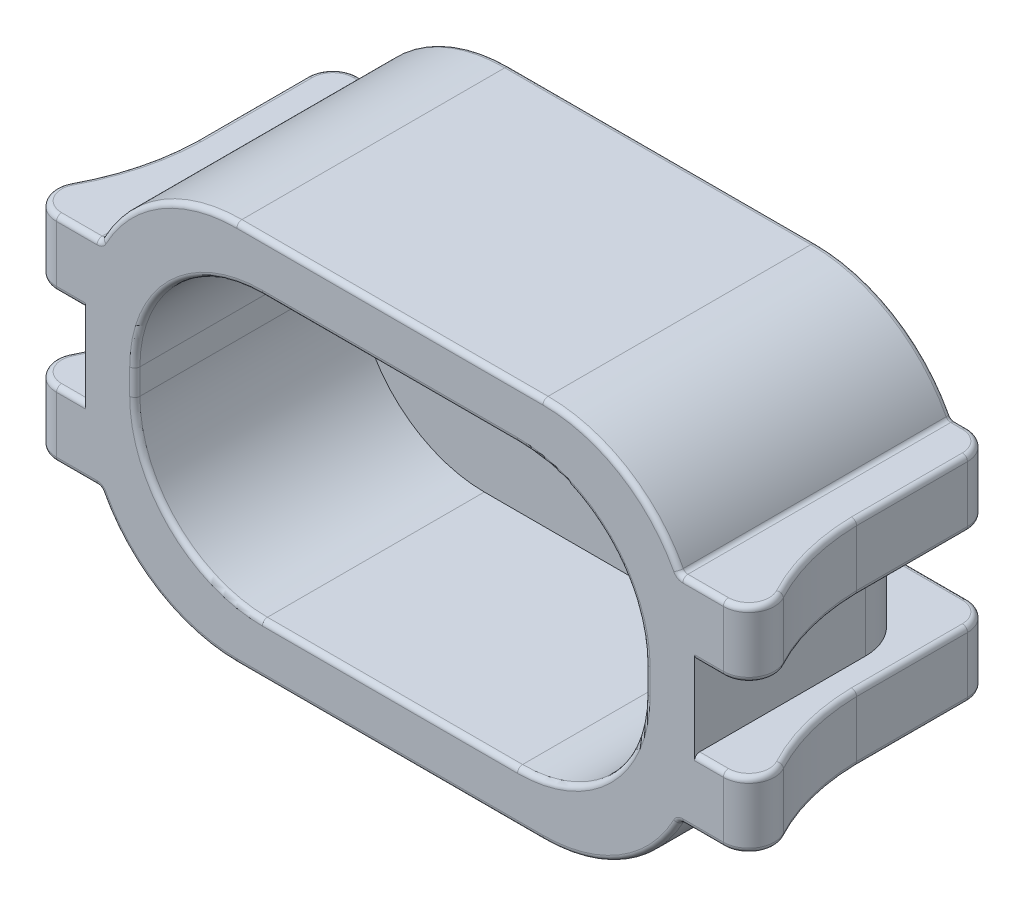
SolidWorks part; units mm, degrees
ref_plane "Front Plane" through (0, 0, 0) normal (0, 0, 1) x (1, 0, 0)
ref_plane "Top Plane" through (0, 0, 0) normal (0, 1, 0) x (1, 0, 0)
ref_plane "Right Plane" through (0, 0, 0) normal (1, 0, 0) x (0, 0, -1)
sketch "Sketch1" plane through (0, 0, 0) normal (0, 0, 1) x (1, 0, 0)
  line L0 (0, -2.7579) -> (0, 2.1887) construction
  line L9 (-3.3744, -0.8) -> (5.2209, -0.8) construction
  line L16 (6, -4.55) -> (-6, -4.55)
  line L17 (6, -4.55) -> (6, 2.95)
  line L18 (6, 2.95) -> (-6, 2.95)
  line L19 (-6, -4.55) -> (-6, 2.95)
  line L20 (6, -4.55) -> (-6, 2.95) construction
  line L21 (6, 2.95) -> (-6, -4.55) construction
  point P5 (0.9233, -0.8)
  point P12 (0, -0.8)
  dimension "D2" = 7.5
extrude "Boss-Extrude1" add sketch "Sketch1" against normal blind 5.35
sketch "Sketch2" plane through (0, 0, 0) normal (0, 0, 1) x (1, 0, 0)
  line L8 (-5, 1.95) -> (-5, -3.55)
  line L9 (-5, -3.55) -> (5, -3.55)
  line L10 (5, -3.55) -> (5, 1.95)
  line L11 (5, 1.95) -> (-5, 1.95)
  line L12 (-5, 1.95) -> (-5, -3.55)
  line L13 (-5, -3.55) -> (5, -3.55)
  line L14 (5, -3.55) -> (5, 1.95)
  line L15 (5, 1.95) -> (-5, 1.95)
  dimension "D1" = 1
extrude "Cut-Extrude1" cut sketch "Sketch2" against normal offset from surface (4.35 mm away) 1 up to face at (0, -0.8, -5.35)
fillet "Fillet3" radius 2.5 4 edges at (-5, 1.95, -2.175) (-5, -3.55, -2.175) (5, -3.55, -2.175) (5, 1.95, -2.175)
fillet "Fillet1" radius 3 4 edges at (6, 2.95, -2.675) (-6, 2.95, -2.675) (-6, -4.55, -2.675) (6, -4.55, -2.675)
sketch "Sketch3" plane through (0, 0, -4.35) normal (0, 0, 1) x (1, 0, 0)
  line L0 (-5, -1.05) -> (-5, -0.55) construction
  line L1 (-5, -1.6) -> (5, -1.6)
  line L2 (-5, -1.6) -> (-5, 0)
  line L3 (-5, 0) -> (5, 0)
  line L4 (5, -1.6) -> (5, 0)
  line L5 (5, -0.55) -> (5, -1.05) construction
  line L6 (10, 0) -> (-10, 0) construction
  line L7 (-6.77, -1.6) -> (-10, -1.6) construction
extrude "Cut-Extrude2" cut sketch "Sketch3" against normal through all
sketch "Sketch4" plane through (0, -1.6, 0) normal (0, -1, 0) x (1, 0, 0)
  line L16 (5.97, -3.35) -> (5.97, 0)
  line L17 (4.27, -4.35) -> (4.97, -4.35)
  line L21 (-4.97, -4.35) -> (-4.27, -4.35)
  line L22 (-5.97, -3.35) -> (-5.97, 0)
  line L24 (4.27, -4.35) -> (-4.27, -4.35)
  line L25 (5.97, 0) -> (-5.97, 0)
  arc A17 (4.97, -4.35) -> (5.97, -3.35) centre (4.97, -3.35) ccw
  arc A22 (-5.97, -3.35) -> (-4.97, -4.35) centre (-4.97, -3.35) ccw
extrude "Cut-Extrude3" cut sketch "Sketch4" against normal blind 1.6 flip side to cut
sketch "Sketch6" plane through (5.97, 0, 0) normal (1, 0, 0) x (0, 0, -1)
  line L0 (0, -1.6) -> (5.35, -1.6) construction
  line L1 (0, -1.6) -> (5.35, -1.6)
  line L2 (0, -1.6) -> (0, -4.55) construction
  line L3 (0, -1.6) -> (0, -2.9)
  line L4 (5.35, -4.55) -> (5.35, -1.6) construction
  line L5 (5.35, -2.9) -> (5.35, -1.6)
  line L6 (0, -2.9) -> (5.35, -2.9)
  dimension "D1" = 1.3
extrude "Boss-Extrude2" add sketch "Sketch6" along normal blind 0.5 and the other way up to next
sketch "Sketch11" plane through (0, -1.6, 0) normal (0, 1, 0) x (1, 0, 0)
  line L0 (6.47, 0) -> (7.47, 0)
  line L1 (6.47, 5.35) -> (6.47, 0) construction
  line L2 (6.47, 2.675) -> (6.47, 0)
  arc A0 (7.47, 0) -> (6.47, 2.675) centre (10.7942, 2.7671) cw
  dimension "D1" = 1
extrude "Boss-Extrude8" add sketch "Sketch11" against normal up to surface (1.3 mm away) up to face at (6.0745, -2.9, -2.675)
ref_plane "Plane1" through (0, -0.8, 0) normal (0, 1, 0) x (1, 0, 0)
ref_plane "Plane2" through (0, 0, 0) normal (1, 0, 0) x (0, -1, 0)
mirror "Mirror1" about plane through (0, -0.8, 0) normal (0, 1, 0) of "Boss-Extrude8", "Boss-Extrude2"
mirror "Mirror2" about plane through (0, 0, 0) normal (1, 0, 0) of "Mirror1", "Boss-Extrude2", "Boss-Extrude8"
fillet "Fillet7" radius 0.5 8 edges at (6.47, -2.25, -5.35) (7.47, -2.25, 0) (6.47, 0.65, -5.35) (7.47, 0.65, 0) (-6.47, 0.65, -5.35) (-7.47, 0.65, 0) (-6.47, -2.25, -5.35) (-7.47, -2.25, 0)
fillet "Fillet4" radius 0.1 4 edges at (5.6791, -2.9, -2.675) (5.6791, 1.3, -2.675) (-5.6791, -2.9, -2.675) (-5.6791, 1.3, -2.675)
fillet "Fillet6" radius 0.1 66 edges at (6.2524, -1.6, 0) (6.2524, 0, 0) (6.47, -2.9, -3.7625) (6.47, 1.3, -3.7625) (-6.47, 1.3, -3.7625) (-6.47, -2.9, -3.7625) (-6.47, 0, -3.7625) (0, 0, -5.35) (6.47, 0, -3.7625) (6.6091, 0, -1.6752) (-6.2524, 0, 0) (-6.6091, 0, -1.6752) (6.3236, 0, -5.2036) (6.9634, 0, -0.2426) (-6.9634, 0, -0.2426) (-6.3236, 0, -5.2036) (-6.6091, 1.3, -1.6752) (-6.9634, 1.3, -0.2426) (-6.3236, 1.3, -5.2036) (0, -1.6, -5.35) (6.6091, -1.6, -1.6752) (6.47, -1.6, -3.7625) (-6.47, -1.6, -3.7625) (-6.6091, -1.6, -1.6752) (-6.2524, -1.6, 0) (6.3236, -1.6, -5.2036) (6.9634, -1.6, -0.2426) (-6.9634, -1.6, -0.2426) (-6.3236, -1.6, -5.2036) (-6.6091, -2.9, -1.6752) (-6.9634, -2.9, -0.2426) (-6.3236, -2.9, -5.2036) (6.6091, 1.3, -1.6752) (6.3236, 1.3, -5.2036) (6.9634, 1.3, -0.2426) (6.6091, -2.9, -1.6752) (6.3236, -2.9, -5.2036) (6.9634, -2.9, -0.2426) (4.5476, -4.12, -5.35) (6.1374, -2.9, 0) (5.855, -2.9, -5.35) (6.1374, 1.3, 0) (5.855, 1.3, -5.35) (4.5476, 2.52, 0) (-5.855, -2.9, -5.35) (-6.1374, -2.9, 0) (-4.5476, -4.12, 0) (-4.5476, 2.52, -5.35) (-5.855, 1.3, -5.35) (-6.1374, 1.3, 0) (5.6884, -2.9143, 0) (5.6884, -2.9143, -5.35) (5.6884, 1.3143, 0) (5.6884, 1.3143, -5.35) (-5.6884, -2.9143, 0) (-5.6884, -2.9143, -5.35) (-5.6884, 1.3143, 0) (-5.6884, 1.3143, -5.35) (0, -4.55, 0) (0, 2.95, 0) (4.5476, -4.12, 0) (-4.5476, 2.52, 0) (0, 2.95, -5.35) (0, -4.55, -5.35) (-4.5476, -4.12, -5.35) (4.5476, 2.52, -5.35)
fillet "Fillet8" radius 0.1 8 edges at (-4.2678, 1.2178, 0) (-5, -0.8, 0) (-4.2678, -2.8178, 0) (0, -3.55, 0) (4.2678, -2.8178, 0) (5, -0.8, 0) (4.2678, 1.2178, 0) (0, 1.95, 0)
